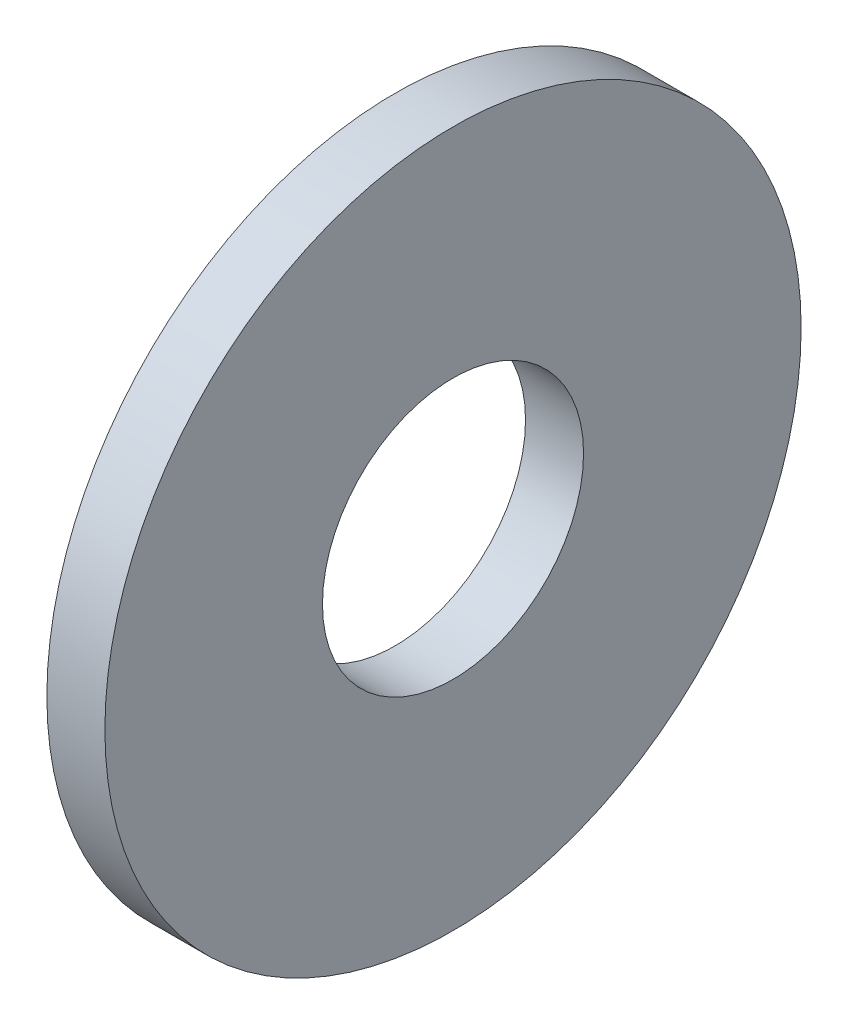
SolidWorks part; units mm, degrees
ref_plane "Front Plane" through (0, 0, 0) normal (0, 0, 1) x (1, 0, 0)
ref_plane "Top Plane" through (0, 0, 0) normal (0, 1, 0) x (1, 0, 0)
ref_plane "Right Plane" through (0, 0, 0) normal (1, 0, 0) x (0, 0, -1)
sketch "Sketch1" plane through (0, 0, 0) normal (1, 0, 0) x (0, 0, -1)
  circle A0 centre (0, 0) radius 14.2875
  circle A1 centre (0, 0) radius 38.1
  dimension "D1" = 28.575
  dimension "D2" = 76.2
extrude "Boss-Extrude1" add sketch "Sketch1" along normal mid plane 6.35
